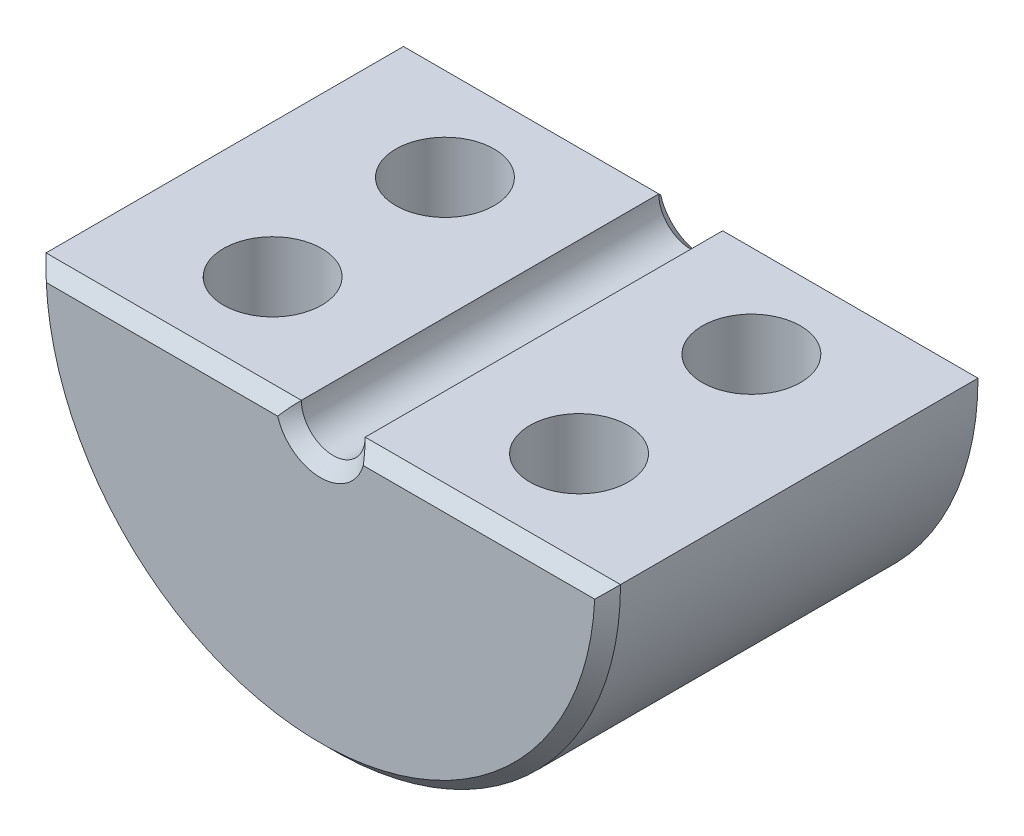
SolidWorks part; units mm, degrees
ref_plane "Front Plane" through (0, 0, 0) normal (0, 0, 1) x (1, 0, 0)
ref_plane "Top Plane" through (0, 0, 0) normal (0, 1, 0) x (1, 0, 0)
ref_plane "Right Plane" through (0, 0, 0) normal (1, 0, 0) x (0, 0, -1)
sketch "Sketch9" plane through (0, 0, 0) normal (0, 0, 1) x (1, 0, 0)
  line L0 (-11.43, 0) -> (-1.27, 0)
  line L1 (1.27, 0) -> (11.43, 0)
  arc A0 (-11.43, 0) -> (11.43, 0) centre (0, 0) ccw
  arc A1 (-1.27, 0) -> (1.27, 0) centre (0, 0) ccw
  point P7 (0, 0)
  dimension "D1" = 22.86
  dimension "D2" = 2.54
extrude "Boss-Extrude2" add sketch "Sketch9" along normal blind 15.24
chamfer "Chamfer1" distance 0.508 angle 45 4 edges at (-6.35, 0, 0) (0, -11.43, 0) (6.35, 0, 0) (0, -1.27, 0)
chamfer "Chamfer2" distance 0.508 angle 45 4 edges at (6.35, 0, 15.24) (0, -11.43, 15.24) (-6.35, 0, 15.24) (0, -1.27, 15.24)
sketch "Sketch13" plane through (0, 0, 0) normal (0, 1, 0) x (1, 0, 0)
  line L3 (0, 0) -> (0, -12.2911) construction
  line L6 (-11.43, -14.732) -> (-1.27, -14.732) construction
  line L7 (-1.27, -0.508) -> (-11.43, -0.508) construction
  circle A0 centre (-6.096, -4.191) radius 1.9558
  circle A1 centre (-6.096, -11.049) radius 1.9558
  circle A2 centre (6.096, -11.049) radius 1.9558
  circle A3 centre (6.096, -4.191) radius 1.9558
  point P3 (0, 0)
  dimension "D1" = 3.9116
  dimension "D4" = 3.9116
  dimension "D2" = 6.096
  dimension "D3" = 3.683
  dimension "D5" = 6.096
  dimension "D6" = 3.683
extrude "Cut-Extrude1" cut sketch "Sketch13" against normal blind 7.62
